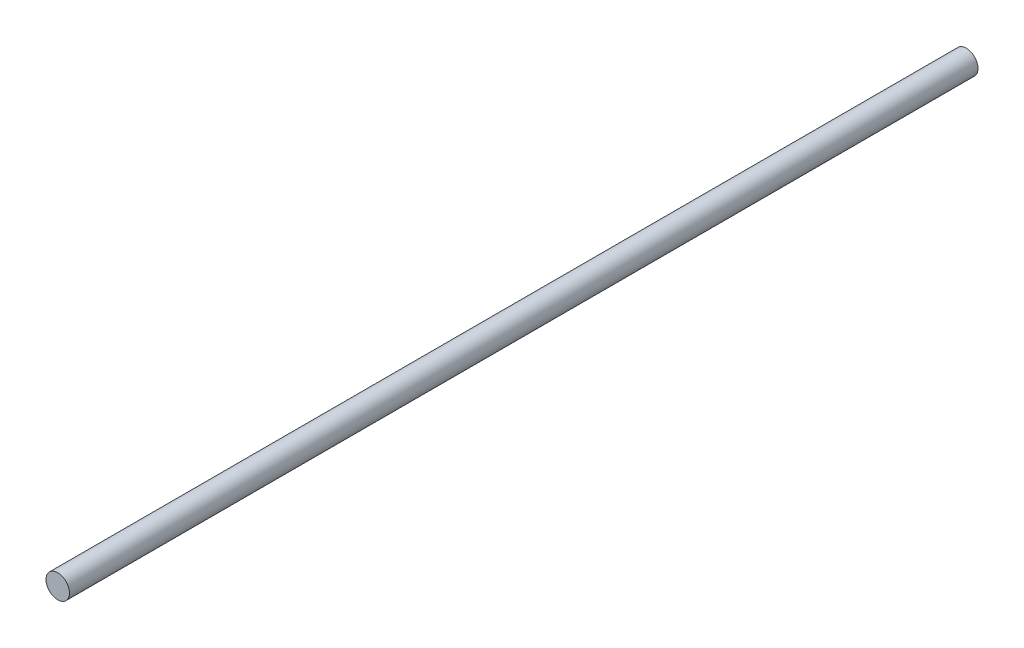
SolidWorks part; units mm, degrees
ref_plane "前视基准面" through (0, 0, 0) normal (0, 0, 1) x (1, 0, 0)
ref_plane "上视基准面" through (0, 0, 0) normal (0, 1, 0) x (1, 0, 0)
ref_plane "右视基准面" through (0, 0, 0) normal (1, 0, 0) x (0, 0, -1)
sketch "Sketch1" plane through (0, 0, 0) normal (0, 0, 1) x (1, 0, 0)
  circle A0 centre (-1.2317, 13.7352) radius 5
extrude "Boss-Extrude1" add sketch "Sketch1" against normal up to surface (387 mm away)
